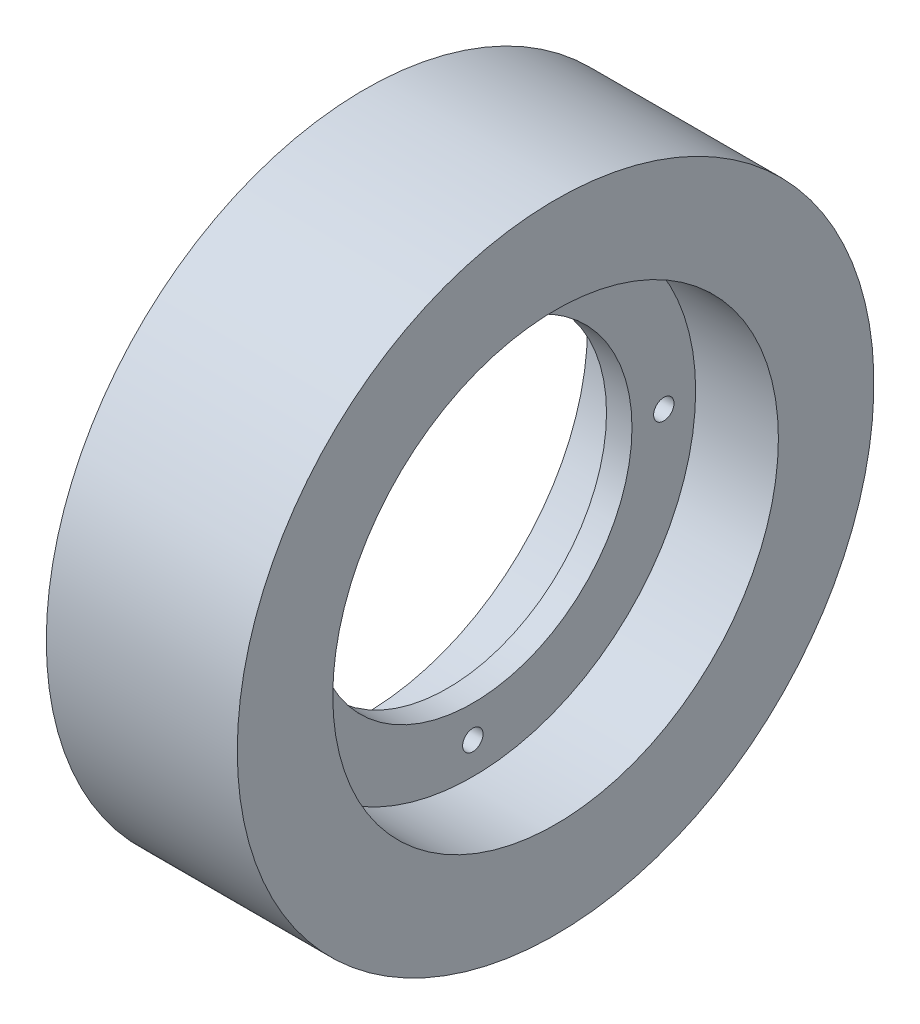
SolidWorks part; units mm, degrees
material "AISI 1020"
ref_plane "Front Plane" through (0, 0, 0) normal (0, 0, 1) x (1, 0, 0)
ref_plane "Top Plane" through (0, 0, 0) normal (0, 1, 0) x (1, 0, 0)
ref_plane "Right Plane" through (0, 0, 0) normal (1, 0, 0) x (0, 0, -1)
sketch "Sketch2" plane through (0, 0, 0) normal (0, 0, 1) x (1, 0, 0)
  line L0 (15, 50) -> (-15, 50)
  line L1 (15, 50) -> (15, 35)
  line L2 (15, 35) -> (2, 35)
  line L3 (2, 35) -> (2, 25)
  line L4 (2, 25) -> (-2, 25)
  line L5 (-2, 25) -> (-2, 35)
  line L6 (-2, 35) -> (-15, 35)
  line L7 (-15, 35) -> (-15, 50)
  line L8 (0, 0) -> (50000, 0) construction
  point P3 (0, 50)
  dimension "D1" = 30
  dimension "D2" = 50
  dimension "D3" = 13
  dimension "D4" = 35
  dimension "D5" = 25
revolve "Revolve1" add sketch "Sketch2" angle 360 about L8
sketch "Sketch3" plane through (2, 0, 0) normal (1, 0, 0) x (0, 0, -1)
  circle A0 centre (0, 30) radius 1.6
  circle A1 centre (0, 0) radius 30 construction
  dimension "D1" = 60
  dimension "D2" = 3.2
extrude "Cut-Extrude1" cut sketch "Sketch3" against normal through all
pattern_circular "CirPattern1" count 4 over 360 about axis through (0, 0, 0) along (1, 0, 0) of "Cut-Extrude1"
